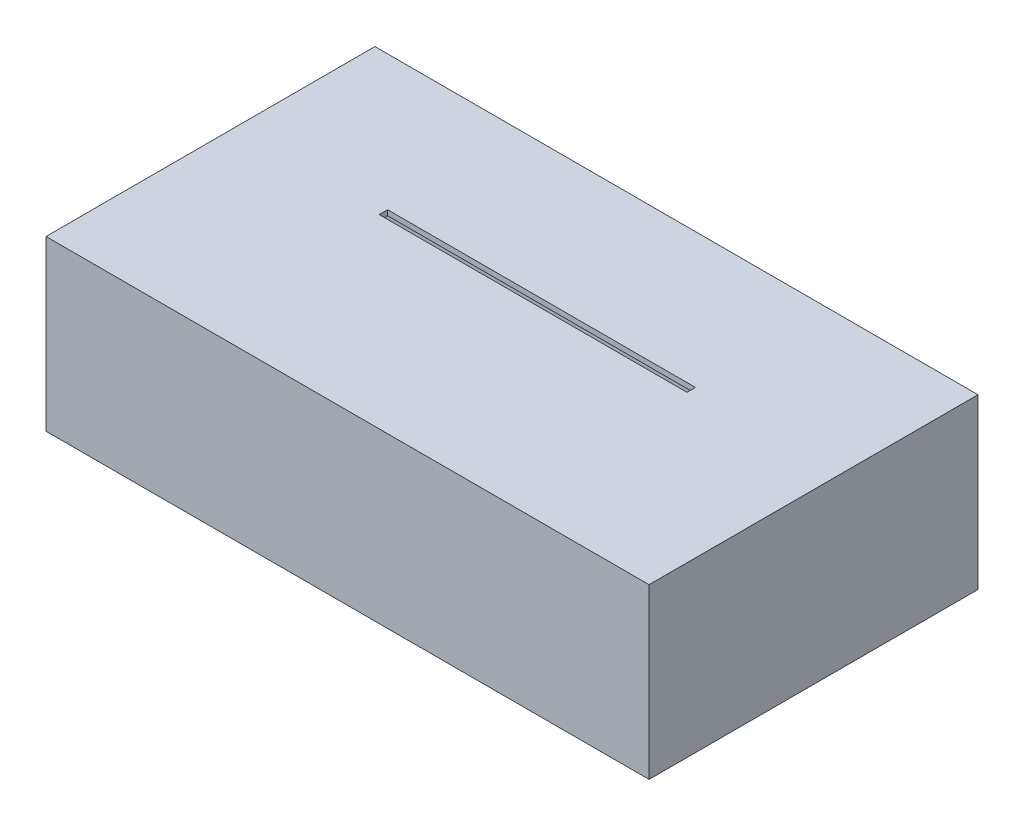
SolidWorks part; units mm, degrees
ref_plane "Front Plane" through (0, 0, 0) normal (0, 0, 1) x (1, 0, 0)
ref_plane "Top Plane" through (0, 0, 0) normal (0, 1, 0) x (1, 0, 0)
ref_plane "Right Plane" through (0, 0, 0) normal (1, 0, 0) x (0, 0, -1)
sketch "Sketch1" plane through (0, 0, 0) normal (0, 1, 0) x (1, 0, 0)
  line L1 (-227.0125, 123.825) -> (227.0125, 123.825)
  line L2 (-227.0125, 123.825) -> (-227.0125, -123.825)
  line L3 (-227.0125, -123.825) -> (227.0125, -123.825)
  line L4 (227.0125, 123.825) -> (227.0125, -123.825)
  point P4 (0, -123.825)
  point P7 (227.0125, 0)
  dimension "D1" = 454.025
  dimension "D2" = 247.65
extrude "Boss-Extrude1" add sketch "Sketch1" along normal blind 127
shell "Shell1" thickness 3.937
sketch "Sketch3" plane through (0, 127, 0) normal (0, 1, 0) x (1, 0, 0)
  line L0 (-227.0125, -123.825) -> (227.0125, -123.825) construction
  line L1 (-115.8875, 22.225) -> (115.8875, 22.225)
  line L2 (-115.8875, 22.225) -> (-115.8875, 15.875)
  line L3 (-115.8875, 15.875) -> (115.8875, 15.875)
  line L4 (115.8875, 22.225) -> (115.8875, 15.875)
  point P6 (0, 15.875)
  dimension "D1" = 139.7
  dimension "D2" = 6.35
  dimension "D3" = 231.775
extrude "Cut-Extrude1" cut sketch "Sketch3" against normal through all
sketch "Sketch4" plane through (0, 0, 0) normal (0, -1, 0) x (1, 0, 0)
  line L0 (118.4275, 119.888) -> (118.4275, 108.3936)
  line L1 (223.0755, -119.888) -> (-223.0755, -119.888)
  line L2 (223.0755, -119.888) -> (223.0755, 119.888)
  line L3 (223.0755, 119.888) -> (118.4275, 119.888)
  line L4 (-223.0755, -119.888) -> (-223.0755, 119.888)
  line L5 (118.4275, 108.3936) -> (-118.4275, 108.3936)
  line L6 (-118.4275, 108.3936) -> (-118.4275, 119.888)
  line L7 (-118.4275, 119.888) -> (-223.0755, 119.888)
  line L8 (-115.8875, 108.3936) -> (115.8875, 108.3936) construction
  line L9 (118.4275, 116.5396) -> (118.4275, 119.888) construction
  line L10 (-118.4275, 100.2477) -> (-118.4275, 116.5396) construction
extrude "Boss-Extrude2" add sketch "Sketch4" against normal blind 4.191 separate body
ref_plane "Plane1" through (-115.8875, 0, 0) normal (1, 0, 0) x (0, 0, -1)
sketch "Sketch5" plane through (-115.8875, 0, 0) normal (1, 0, 0) x (0, 0, -1)
  line L0 (-100.2477, 2.413) -> (-18.415, 61.3848)
  line L1 (11.1125, 82.6635) -> (-100.2477, 2.413) construction
  line L2 (-18.415, 61.3848) -> (13.335, 61.3848)
  line L3 (13.335, 83.9038) -> (13.335, 4.953) construction
  line L4 (13.335, 61.3848) -> (13.335, 2.413)
  line L5 (11.1125, 2.413) -> (23.9713, 2.413) construction
  line L6 (13.335, 2.413) -> (-12.065, 2.413)
  line L7 (-12.065, 2.413) -> (-12.065, -1.905)
  line L9 (-12.065, -1.905) -> (-24.765, -1.905)
  line L10 (-24.765, -1.905) -> (-24.765, 2.413)
  line L11 (-24.765, 2.413) -> (-62.1477, 2.413)
  line L12 (-62.1477, 2.413) -> (-62.1477, -1.905)
  line L13 (-62.1477, -1.905) -> (-74.8477, -1.905)
  line L14 (-74.8477, -1.905) -> (-74.8477, 2.413)
  line L15 (-74.8477, 2.413) -> (-100.2477, 2.413)
  dimension "D1" = 4.318
  dimension "D2" = 12.7
  dimension "D3" = 12.7
  dimension "D4" = 25.4
  dimension "D5" = 25.4
  dimension "D6" = 31.75
extrude "Boss-Extrude3" add sketch "Sketch5" along normal blind 4.191 separate body
mirror "Mirror2" about plane through (0, 0, 0) normal (1, 0, 0) of bodies 105
sketch "Sketch6" plane through (0, 0, 0) normal (0, -1, 0) x (1, 0, 0)
  line L0 (-111.6965, 74.8477) -> (-115.8875, 74.8477) construction
  line L1 (-115.8875, 74.8477) -> (-111.6965, 74.8477)
  line L2 (-115.8875, 74.8477) -> (-115.8875, 62.1477)
  line L3 (-115.8875, 62.1477) -> (-111.6965, 62.1477)
  line L4 (-111.6965, 74.8477) -> (-111.6965, 62.1477)
  line L5 (-115.8875, 24.765) -> (-111.6965, 24.765)
  line L6 (-115.8875, 24.765) -> (-115.8875, 12.065)
  line L7 (-115.8875, 12.065) -> (-111.6965, 12.065)
  line L8 (-111.6965, 24.765) -> (-111.6965, 12.065)
  line L9 (111.6965, 24.765) -> (115.8875, 24.765)
  line L10 (111.6965, 24.765) -> (111.6965, 12.065)
  line L11 (111.6965, 12.065) -> (115.8875, 12.065)
  line L12 (115.8875, 24.765) -> (115.8875, 12.065)
  line L13 (111.6965, 74.8477) -> (115.8875, 74.8477)
  line L14 (111.6965, 74.8477) -> (111.6965, 62.1477)
  line L15 (111.6965, 62.1477) -> (115.8875, 62.1477)
  line L16 (115.8875, 74.8477) -> (115.8875, 62.1477)
  line L17 (-111.6965, 74.8477) -> (-111.6965, 62.1477) construction
  line L18 (-115.8875, 74.8477) -> (-115.8875, 62.1477) construction
  line L19 (-111.6965, 62.1477) -> (-115.8875, 62.1477) construction
  line L20 (-111.6965, 24.765) -> (-115.8875, 24.765) construction
  line L21 (-111.6965, 12.065) -> (-115.8875, 12.065) construction
  line L22 (-111.6965, 24.765) -> (-111.6965, 12.065) construction
  line L23 (-115.8875, 24.765) -> (-115.8875, 12.065) construction
  line L24 (111.6965, 12.065) -> (115.8875, 12.065) construction
  line L25 (111.6965, 24.765) -> (115.8875, 24.765) construction
  line L26 (115.8875, 24.765) -> (115.8875, 12.065) construction
  line L27 (111.6965, 24.765) -> (111.6965, 12.065) construction
  line L28 (111.6965, 74.8477) -> (115.8875, 74.8477) construction
  line L29 (111.6965, 62.1477) -> (115.8875, 62.1477) construction
  line L30 (115.8875, 74.8477) -> (115.8875, 62.1477) construction
  line L31 (111.6965, 74.8477) -> (111.6965, 62.1477) construction
  line L32 (-116.6812, -21.4313) -> (-116.6812, -11.1125) construction
  line L33 (115.0938, -23.0188) -> (-115.0937, -23.0188) construction
  line L34 (116.6812, -11.1125) -> (116.6812, -21.4313) construction
  line L35 (-116.6812, -21.4313) -> (-116.6812, -15.875)
  line L36 (115.0938, -23.0188) -> (-115.0937, -23.0188)
  line L37 (116.6812, -15.875) -> (116.6812, -21.4313)
  line L39 (116.6812, -15.875) -> (-116.6812, -15.875)
  line L40 (-115.8875, -15.875) -> (115.8875, -15.875) construction
  arc A0 (-116.6812, -21.4313) -> (-115.0937, -23.0188) centre (-115.0937, -21.4313) ccw construction
  arc A1 (115.0938, -23.0188) -> (116.6812, -21.4313) centre (115.0938, -21.4313) ccw construction
  arc A2 (-116.6812, -21.4313) -> (-115.0937, -23.0188) centre (-115.0937, -21.4313) ccw
  arc A3 (115.0938, -23.0188) -> (116.6812, -21.4313) centre (115.0938, -21.4313) ccw
extrude "Cut-Extrude2" cut sketch "Sketch6" against normal blind 5.08
